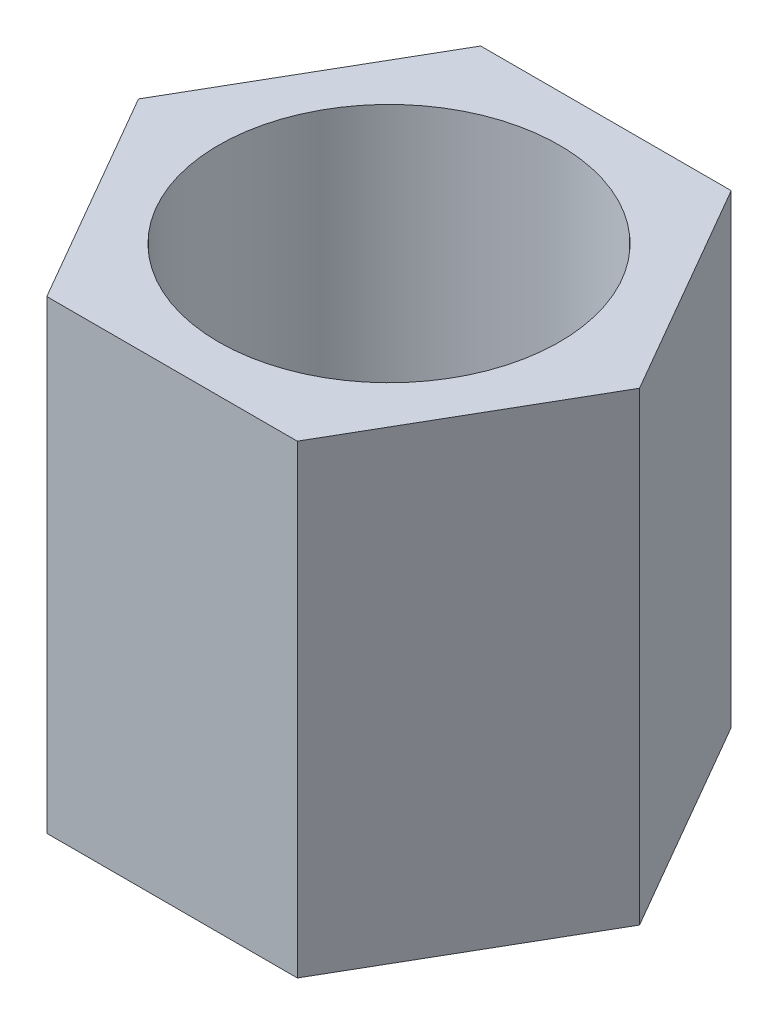
SolidWorks part; units mm, degrees
material "黄铜"
ref_plane "前视基准面" through (0, 0, 0) normal (0, 0, 1) x (1, 0, 0)
ref_plane "上视基准面" through (0, 0, 0) normal (0, 1, 0) x (1, 0, 0)
ref_plane "右视基准面" through (0, 0, 0) normal (1, 0, 0) x (0, 0, -1)
sketch "草图1" plane through (0, 0, 0) normal (0, 1, 0) x (1, 0, 0)
  line L1 (1.6166, 0) -> (0.8083, 1.4)
  line L2 (0.8083, 1.4) -> (-0.8083, 1.4)
  line L3 (-0.8083, 1.4) -> (-1.6166, 0)
  line L4 (-1.6166, 0) -> (-0.8083, -1.4)
  line L5 (-0.8083, -1.4) -> (0.8083, -1.4)
  line L6 (0.8083, -1.4) -> (1.6166, 0)
  circle A0 centre (0, 0) radius 1.4 construction
  dimension "D1" = 2.8
extrude "凸台-拉伸1" add sketch "草图1" along normal blind 3
sketch "草图2" plane through (0, 3, 0) normal (0, 1, 0) x (1, 0, 0)
  circle A0 centre (0, 0) radius 1.1
  dimension "D1" = 2.2
extrude "切除-拉伸1" cut sketch "草图2" against normal through all
